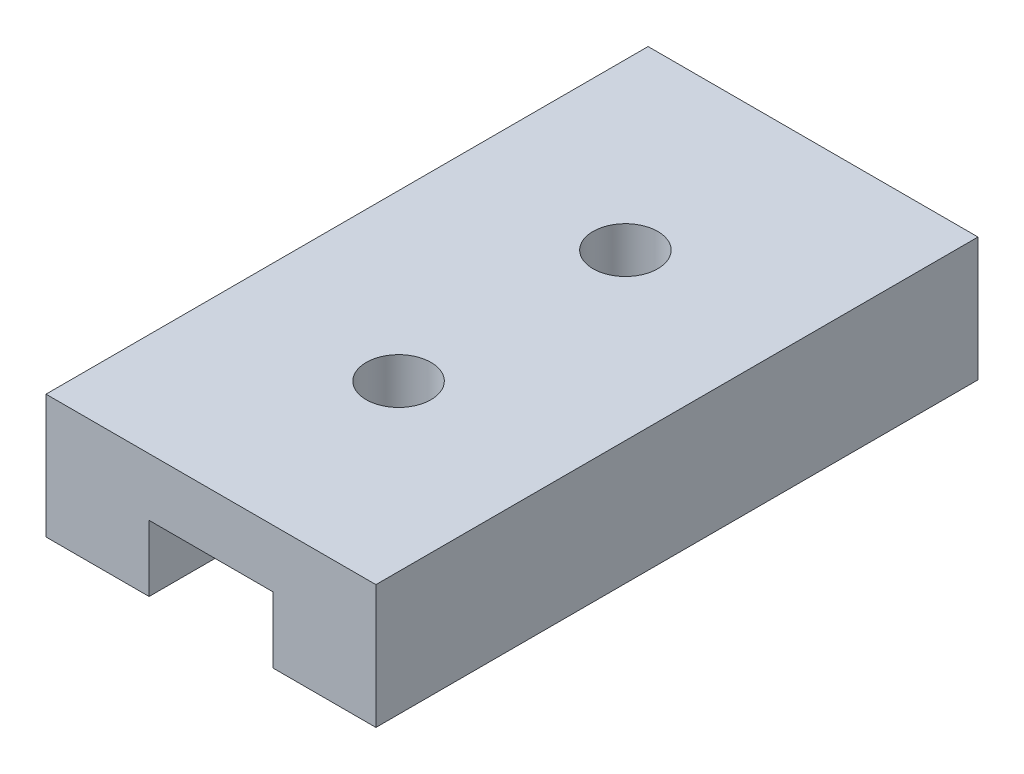
SolidWorks part; units mm, degrees
ref_plane "Front Plane" through (0, 0, 0) normal (0, 0, 1) x (1, 0, 0)
ref_plane "Top Plane" through (0, 0, 0) normal (0, 1, 0) x (1, 0, 0)
ref_plane "Right Plane" through (0, 0, 0) normal (1, 0, 0) x (0, 0, -1)
sketch "Sketch1" plane through (0, 0, 0) normal (0, 0, 1) x (1, 0, 0)
  line L0 (-1.5, 0) -> (-4, 0)
  line L1 (-4, 0) -> (-4, 3)
  line L2 (-4, 3) -> (4, 3)
  line L3 (4, 3) -> (4, 0)
  line L4 (4, 0) -> (1.5, 0)
  line L5 (1.5, 0) -> (1.5, 1.6)
  line L6 (1.5, 1.6) -> (-1.5, 1.6)
  line L7 (-1.5, 1.6) -> (-1.5, 0)
  point P3 (0, 3)
  point P10 (-1.5, 1.5449)
  dimension "D1" = 2.5
  dimension "D2" = 3
  dimension "D3" = 8
  dimension "D4" = 1.6
extrude "Boss-Extrude1" add sketch "Sketch1" along normal blind 14.6
sketch "Sketch2" plane through (0, 3, 0) normal (0, 1, 0) x (1, 0, 0)
  line L0 (0, -4.55) -> (0, -10.05) construction
  line L1 (4, -14.6) -> (4, 0) construction
  circle A0 centre (0, -10.05) radius 0.785
  circle A1 centre (0, -4.55) radius 0.785
  point P7 (4, -7.3)
  point P8 (0, -7.3)
  dimension "D2" = 1.57
  dimension "D1" = 5.5
extrude "Cut-Extrude1" cut sketch "Sketch2" against normal through all
